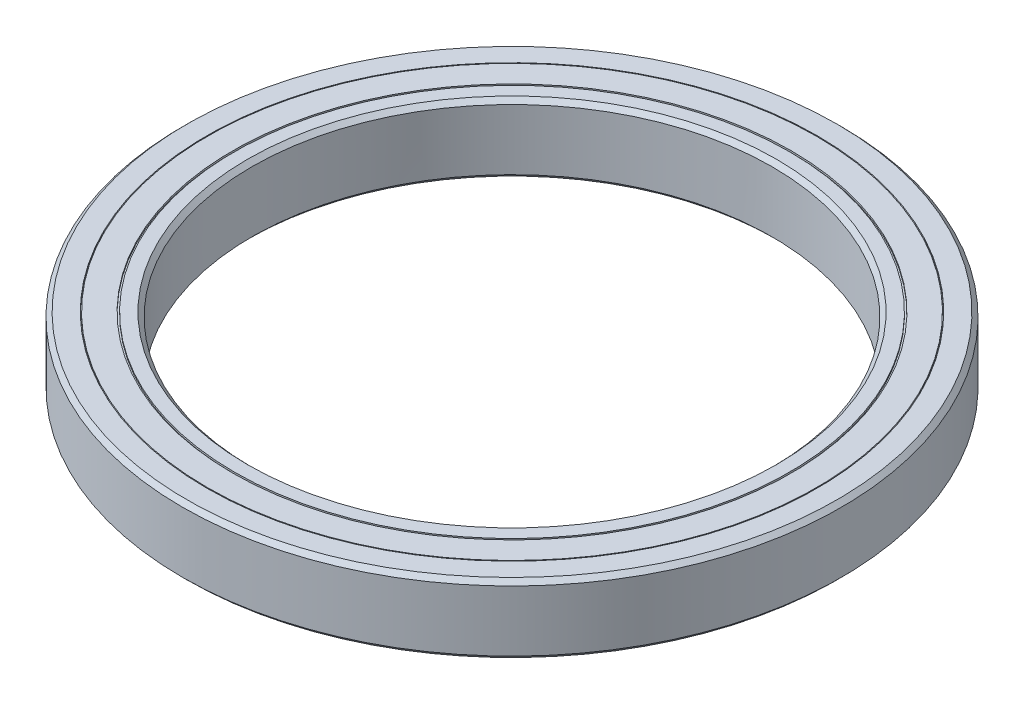
SolidWorks part; units mm, degrees
material "不锈钢 (铁素体)"
ref_plane "前视基准面" through (0, 0, 0) normal (0, 0, 1) x (1, 0, 0)
ref_plane "上视基准面" through (0, 0, 0) normal (0, 1, 0) x (1, 0, 0)
ref_plane "右视基准面" through (0, 0, 0) normal (1, 0, 0) x (0, 0, -1)
sketch "草图1" plane through (0, 0, 0) normal (0, 0, 1) x (1, 0, 0)
  line L0 (0, 60.4596) -> (0, -64.46) construction
  line L1 (87.4619, 0) -> (-122.1921, 0) construction
  line L2 (30, -4) -> (30, 4)
  line L8 (38, 4) -> (38, -4)
  line L14 (30, 4) -> (32, 4)
  line L15 (32, 4) -> (32, 3.8)
  line L16 (32, 3.8) -> (32.2, 3.8)
  line L18 (32.2, 3.8) -> (32.2, 4)
  line L19 (32.2, 4) -> (35.1, 4)
  line L20 (35.1, 4) -> (35.1, 3.8)
  line L21 (35.1, 3.8) -> (35.2, 3.8)
  line L22 (35.2, 3.8) -> (35.2, 4)
  line L23 (35.2, 4) -> (38, 4)
  line L24 (35.2, -4) -> (38, -4)
  line L25 (35.2, -3.8) -> (35.2, -4)
  line L26 (35.1, -3.8) -> (35.2, -3.8)
  line L27 (35.1, -4) -> (35.1, -3.8)
  line L28 (32.2, -4) -> (35.1, -4)
  line L29 (32.2, -3.8) -> (32.2, -4)
  line L30 (32, -3.8) -> (32.2, -3.8)
  line L31 (32, -4) -> (32, -3.8)
  line L32 (30, -4) -> (32, -4)
  dimension "D1" = 30
  dimension "D2" = 38
  dimension "D3" = 2
  dimension "D4" = 0.2
  dimension "D5" = 3
  dimension "D6" = 0.1
  dimension "D7" = 0.2
  dimension "D8" = 4
revolve "旋转1" add sketch "草图1" angle 360 about L0
chamfer "倒角1" distance 0.5 angle 45 4 edges at (0, -4, 38) (0, 4, 38) (0, -4, 30) (0, 4, 30)
